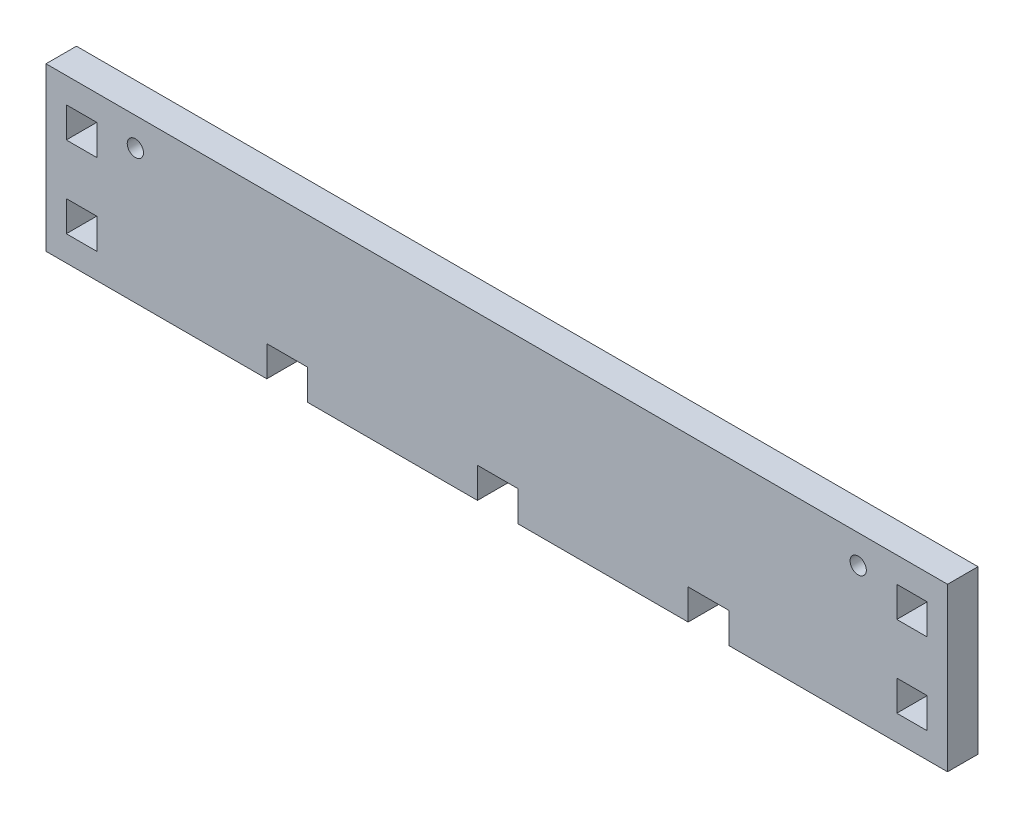
SolidWorks part; units mm, degrees
ref_plane "Front Plane" through (0, 0, 0) normal (0, 0, 1) x (1, 0, 0)
ref_plane "Top Plane" through (0, 0, 0) normal (0, 1, 0) x (1, 0, 0)
ref_plane "Right Plane" through (0, 0, 0) normal (1, 0, 0) x (0, 0, -1)
sketch "Sketch1" plane through (0, 0, 0) normal (0, 0, 1) x (1, 0, 0)
  line L0 (0, 0) -> (0, 80)
  line L1 (0, 80) -> (444, 80)
  line L2 (444, 80) -> (444, 0)
  line L3 (0, 0) -> (108.75, 0)
  line L4 (108.75, 0) -> (108.75, 15)
  line L5 (108.75, 15) -> (128.75, 15)
  line L6 (128.75, 15) -> (128.75, 0)
  line L7 (128.75, 0) -> (212.5, 0)
  line L8 (212.5, 0) -> (212.5, 15)
  line L9 (212.5, 15) -> (232.5, 15)
  line L10 (232.5, 15) -> (232.5, 0)
  line L11 (232.5, 0) -> (316.25, 0)
  line L12 (316.25, 0) -> (316.25, 15)
  line L13 (316.25, 15) -> (336.25, 15)
  line L14 (336.25, 15) -> (336.25, 0)
  line L15 (336.25, 0) -> (444, 0)
  line L16 (222, 80) -> (222, 62.9333) construction
  line L17 (10, 67.5) -> (25, 67.5)
  line L18 (10, 67.5) -> (10, 52.5)
  line L19 (10, 52.5) -> (25, 52.5)
  line L20 (25, 67.5) -> (25, 52.5)
  line L21 (10, 27.5) -> (25, 27.5)
  line L22 (10, 27.5) -> (10, 12.5)
  line L23 (10, 12.5) -> (25, 12.5)
  line L24 (25, 27.5) -> (25, 12.5)
  line L25 (419, 27.5) -> (419, 12.5)
  line L26 (434, 12.5) -> (419, 12.5)
  line L27 (434, 27.5) -> (434, 12.5)
  line L28 (434, 27.5) -> (419, 27.5)
  line L29 (419, 67.5) -> (419, 52.5)
  line L30 (434, 52.5) -> (419, 52.5)
  line L31 (434, 67.5) -> (434, 52.5)
  line L32 (434, 67.5) -> (419, 67.5)
  circle A0 centre (44, 66) radius 4
  circle A1 centre (400, 66) radius 4
  dimension "D23" = 8
  dimension "D1" = 80
  dimension "D2" = 444
  dimension "D3" = 80
  dimension "D4" = 108.75
  dimension "D5" = 15
  dimension "D6" = 15
  dimension "D7" = 20
  dimension "D8" = 83.75
  dimension "D9" = 15
  dimension "D10" = 15
  dimension "D11" = 20
  dimension "D12" = 83.75
  dimension "D13" = 20
  dimension "D14" = 15
  dimension "D15" = 15
  dimension "D16" = 15
  dimension "D17" = 15
  dimension "D18" = 15
  dimension "D19" = 25
  dimension "D20" = 12.5
  dimension "D21" = 10
  dimension "D22" = 10
  dimension "D24" = 14
  dimension "D25" = 44
extrude "Boss-Extrude1" add sketch "Sketch1" along normal blind 15
